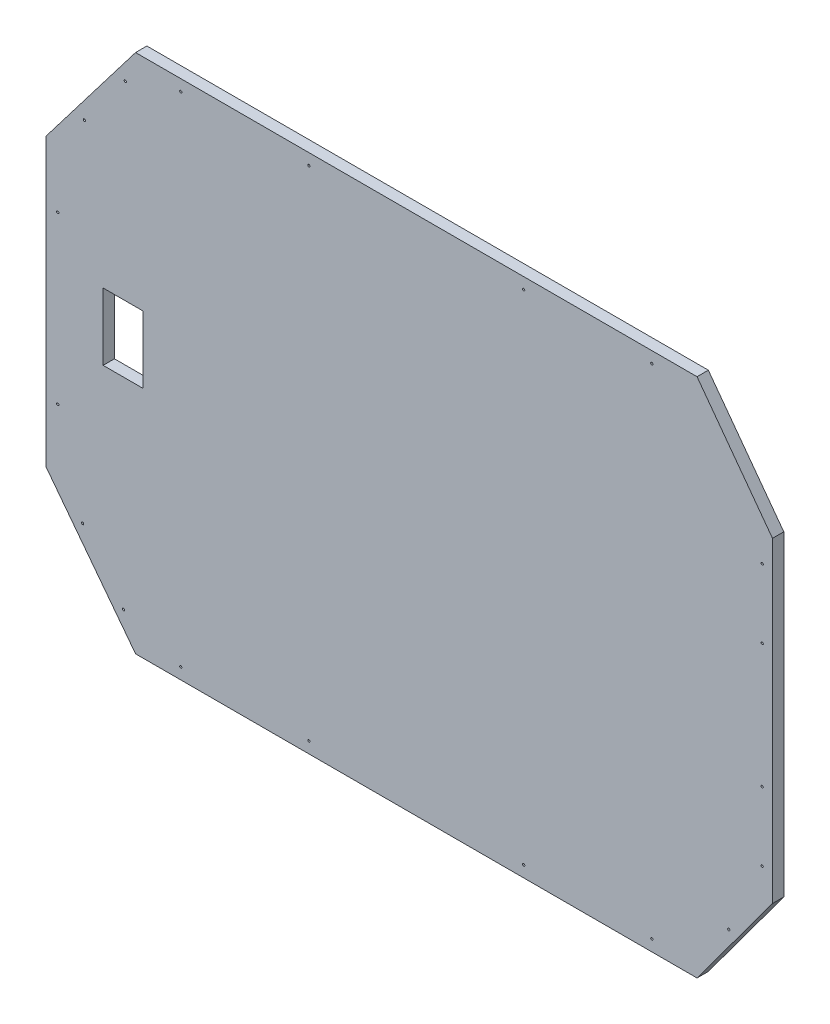
SolidWorks part; units mm, degrees
ref_plane "Front Plane" through (0, 0, 0) normal (0, 0, 1) x (1, 0, 0)
ref_plane "Top Plane" through (0, 0, 0) normal (0, 1, 0) x (1, 0, 0)
ref_plane "Right Plane" through (0, 0, 0) normal (1, 0, 0) x (0, 0, -1)
sketch "Sketch1" plane through (0, 0, 0) normal (0, 0, 1) x (1, 0, 0)
  line L0 (118.58, 345.4877) -> (863.58, 345.4877) construction
  line L1 (0, 500.6804) -> (118.58, 345.4877) construction
  line L2 (0, 881.2704) -> (0, 500.6804) construction
  line L3 (118.58, 1036.4632) -> (0, 881.2704) construction
  line L4 (863.58, 1036.4632) -> (118.58, 1036.4632) construction
  line L5 (963.71, 900.8043) -> (863.58, 1036.4632) construction
  line L6 (963.71, 481.1465) -> (963.71, 900.8043) construction
  line L7 (863.58, 345.4877) -> (963.71, 481.1465) construction
  line L8 (118.58, 345.4877) -> (863.58, 345.4877)
  line L9 (0, 500.6804) -> (118.58, 345.4877)
  line L10 (0, 881.2704) -> (0, 500.6804)
  line L11 (118.58, 1036.4632) -> (0, 881.2704)
  line L12 (863.58, 1036.4632) -> (118.58, 1036.4632)
  line L13 (963.71, 900.8043) -> (863.58, 1036.4632)
  line L14 (963.71, 481.1465) -> (963.71, 900.8043)
  line L15 (863.58, 345.4877) -> (963.71, 481.1465)
  line L60 (44.2234, 939.1483) -> (2.5279, 884.5789)
  line L62 (44.2234, 939.1483) -> (2.5279, 884.5789)
  line L64 (2.5279, 884.5789) -> (2.5279, 710.9754)
  line L66 (2.5279, 884.5789) -> (2.5279, 710.9754)
  line L68 (2.5279, 710.9754) -> (32.5279, 710.9754)
  line L70 (52.236, 458.7868) -> (91.9659, 489.1436)
  line L71 (91.9659, 489.1436) -> (128.8173, 440.9139)
  line L72 (128.8173, 440.9139) -> (81.1415, 404.4857)
  line L73 (2.5279, 710.9754) -> (32.5279, 710.9754)
  line L75 (247.5279, 355.4877) -> (247.5279, 421.1462)
  line L76 (247.5279, 421.1462) -> (301.5406, 421.1462)
  line L77 (301.5406, 421.1462) -> (301.5406, 355.4877)
  line L78 (32.5279, 710.9754) -> (32.5279, 680.9754)
  line L80 (32.5279, 710.9754) -> (32.5279, 680.9754)
  line L82 (32.5279, 680.9754) -> (2.5279, 680.9754)
  line L83 (501.5406, 355.4877) -> (501.5406, 421.1462)
  line L84 (501.5406, 421.1462) -> (555.5406, 421.1462)
  line L85 (555.5406, 421.1462) -> (555.5406, 355.4877)
  line L87 (32.5279, 680.9754) -> (2.5279, 680.9754)
  line L88 (894.7004, 404.4193) -> (852.6416, 435.4629)
  line L89 (852.6416, 435.4629) -> (885.5391, 480.0333)
  line L90 (885.5391, 480.0333) -> (927.5979, 448.9897)
  line L92 (2.5279, 680.9754) -> (2.5279, 507.372)
  line L94 (2.5279, 680.9754) -> (2.5279, 507.372)
  line L96 (2.5279, 507.372) -> (44.2234, 452.8026)
  line L98 (927.5979, 942.9612) -> (885.5391, 911.9176)
  line L99 (885.5391, 911.9176) -> (852.6416, 956.4879)
  line L100 (852.6416, 956.4879) -> (894.7004, 987.5316)
  line L101 (2.5279, 507.372) -> (44.2234, 452.8026)
  line L103 (555.5406, 1036.4632) -> (555.5406, 970.8046)
  line L104 (555.5406, 970.8046) -> (501.5406, 970.8046)
  line L105 (501.5406, 970.8046) -> (501.5406, 1036.4632)
  line L106 (44.2234, 452.8026) -> (52.1694, 458.874)
  line L108 (44.2234, 452.8026) -> (52.1694, 458.874)
  line L110 (52.1694, 458.874) -> (52.236, 458.7868)
  line L111 (301.5406, 1036.4632) -> (301.5406, 970.8046)
  line L112 (301.5406, 970.8046) -> (247.5279, 970.8046)
  line L113 (247.5279, 970.8046) -> (247.5279, 1036.4632)
  line L115 (52.1694, 458.874) -> (52.236, 458.7868)
  line L116 (81.1415, 987.4652) -> (128.8173, 951.0369)
  line L117 (128.8173, 951.0369) -> (91.9659, 902.8072)
  line L118 (91.9659, 902.8072) -> (52.236, 933.1641)
  line L130 (52.236, 458.7868) -> (91.9659, 489.1436)
  line L131 (91.9659, 489.1436) -> (128.8173, 440.9139)
  line L132 (128.8173, 440.9139) -> (81.1415, 404.4857)
  line L135 (247.5279, 355.4877) -> (247.5279, 421.1462)
  line L136 (247.5279, 421.1462) -> (301.5406, 421.1462)
  line L137 (301.5406, 421.1462) -> (301.5406, 355.4877)
  line L143 (501.5406, 355.4877) -> (501.5406, 421.1462)
  line L144 (501.5406, 421.1462) -> (555.5406, 421.1462)
  line L145 (555.5406, 421.1462) -> (555.5406, 355.4877)
  line L148 (894.7004, 404.4193) -> (852.6416, 435.4629)
  line L149 (852.6416, 435.4629) -> (885.5391, 480.0333)
  line L150 (885.5391, 480.0333) -> (927.5979, 448.9897)
  line L158 (927.5979, 942.9612) -> (885.5391, 911.9176)
  line L159 (885.5391, 911.9176) -> (852.6416, 956.4879)
  line L160 (852.6416, 956.4879) -> (894.7004, 987.5316)
  line L163 (555.5406, 1036.4632) -> (555.5406, 970.8046)
  line L164 (555.5406, 970.8046) -> (501.5406, 970.8046)
  line L165 (501.5406, 970.8046) -> (501.5406, 1036.4632)
  line L171 (301.5406, 1036.4632) -> (301.5406, 970.8046)
  line L172 (301.5406, 970.8046) -> (247.5279, 970.8046)
  line L173 (247.5279, 970.8046) -> (247.5279, 1036.4632)
  line L176 (81.1415, 987.4652) -> (128.8173, 951.0369)
  line L177 (128.8173, 951.0369) -> (91.9659, 902.8072)
  line L178 (91.9659, 902.8072) -> (52.236, 933.1641)
  line L344 (81.1415, 404.4857) -> (118.58, 355.4877)
  line L346 (81.1415, 404.4857) -> (118.58, 355.4877)
  line L420 (118.58, 355.4877) -> (247.5279, 355.4877)
  line L421 (118.58, 355.4877) -> (247.5279, 355.4877)
  line L422 (301.5406, 355.4877) -> (439.5279, 355.4877)
  line L423 (301.5406, 355.4877) -> (439.5279, 355.4877)
  line L424 (439.5279, 355.4877) -> (439.5279, 385.4877)
  line L425 (439.5279, 355.4877) -> (439.5279, 385.4877)
  line L426 (439.5279, 385.4877) -> (469.5279, 385.4877)
  line L427 (439.5279, 385.4877) -> (469.5279, 385.4877)
  line L428 (469.5279, 385.4877) -> (469.5279, 355.4877)
  line L429 (469.5279, 385.4877) -> (469.5279, 355.4877)
  line L430 (469.5279, 355.4877) -> (501.5406, 355.4877)
  line L431 (469.5279, 355.4877) -> (501.5406, 355.4877)
  line L432 (555.5406, 355.4877) -> (858.5839, 355.4877)
  line L433 (555.5406, 355.4877) -> (858.5839, 355.4877)
  line L434 (858.5839, 355.4877) -> (894.7004, 404.4193)
  line L435 (858.5839, 355.4877) -> (894.7004, 404.4193)
  line L436 (927.5979, 448.9897) -> (956.2379, 487.792)
  line L437 (927.5979, 448.9897) -> (956.2379, 487.792)
  line L438 (956.2379, 487.792) -> (956.2379, 680.9754)
  line L439 (956.2379, 487.792) -> (956.2379, 680.9754)
  line L440 (956.2379, 680.9754) -> (926.2379, 680.9754)
  line L441 (956.2379, 680.9754) -> (926.2379, 680.9754)
  line L442 (926.2379, 680.9754) -> (926.2379, 710.9754)
  line L443 (926.2379, 680.9754) -> (926.2379, 710.9754)
  line L444 (926.2379, 710.9754) -> (956.2379, 710.9754)
  line L445 (926.2379, 710.9754) -> (956.2379, 710.9754)
  line L446 (956.2379, 710.9754) -> (956.2379, 904.1589)
  line L447 (956.2379, 710.9754) -> (956.2379, 904.1589)
  line L448 (956.2379, 904.1589) -> (927.5979, 942.9612)
  line L449 (956.2379, 904.1589) -> (927.5979, 942.9612)
  line L450 (894.7004, 987.5316) -> (858.5839, 1036.4632)
  line L451 (894.7004, 987.5316) -> (858.5839, 1036.4632)
  line L452 (858.5839, 1036.4632) -> (555.5406, 1036.4632)
  line L453 (858.5839, 1036.4632) -> (555.5406, 1036.4632)
  line L454 (501.5406, 1036.4632) -> (469.5279, 1036.4632)
  line L455 (501.5406, 1036.4632) -> (469.5279, 1036.4632)
  line L456 (469.5279, 1036.4632) -> (469.5279, 1006.4632)
  line L457 (469.5279, 1036.4632) -> (469.5279, 1006.4632)
  line L458 (469.5279, 1006.4632) -> (439.5279, 1006.4632)
  line L459 (469.5279, 1006.4632) -> (439.5279, 1006.4632)
  line L460 (439.5279, 1006.4632) -> (439.5279, 1036.4632)
  line L461 (439.5279, 1006.4632) -> (439.5279, 1036.4632)
  line L462 (439.5279, 1036.4632) -> (301.5406, 1036.4632)
  line L463 (439.5279, 1036.4632) -> (301.5406, 1036.4632)
  line L464 (247.5279, 1036.4632) -> (118.58, 1036.4632)
  line L465 (247.5279, 1036.4632) -> (118.58, 1036.4632)
  line L466 (118.58, 1036.4632) -> (81.1415, 987.4652)
  line L467 (118.58, 1036.4632) -> (81.1415, 987.4652)
  line L530 (52.1694, 933.0769) -> (44.2234, 939.1483)
  line L531 (52.1694, 933.0769) -> (44.2234, 939.1483)
  line L532 (52.236, 933.1641) -> (52.1694, 933.0769)
  line L533 (52.236, 933.1641) -> (52.1694, 933.0769)
  circle A0 centre (633.58, 360.4877) radius 1.5 construction
  circle A1 centre (348.58, 360.4877) radius 1.5 construction
  circle A2 centre (178.58, 360.4877) radius 1.5 construction
  arc A3 (101.5789, 389.644) -> (103.3851, 387.2486) centre (102.482, 388.4463) ccw construction
  arc A4 (103.3851, 387.2486) -> (101.5789, 389.644) centre (102.482, 388.4463) ccw construction
  arc A5 (49.1995, 459.109) -> (47.3933, 461.5044) centre (48.2964, 460.3067) ccw construction
  arc A6 (47.3933, 461.5044) -> (49.1995, 459.109) centre (48.2964, 460.3067) ccw construction
  arc A7 (15.3287, 579.1804) -> (15.3287, 582.1804) centre (15.3287, 580.6804) ccw construction
  arc A8 (15.3287, 582.1804) -> (15.3287, 579.1804) centre (15.3287, 580.6804) ccw construction
  arc A9 (15.3287, 799.7704) -> (15.3287, 802.7704) centre (15.3287, 801.2704) ccw construction
  arc A10 (15.3287, 802.7704) -> (15.3287, 799.7704) centre (15.3287, 801.2704) ccw construction
  arc A11 (51.6031, 926.0294) -> (49.7969, 923.6341) centre (50.7, 924.8318) ccw construction
  arc A12 (49.7969, 923.6341) -> (51.6031, 926.0294) centre (50.7, 924.8318) ccw construction
  arc A13 (105.7887, 997.8898) -> (103.9825, 995.4945) centre (104.8856, 996.6922) ccw construction
  arc A14 (103.9825, 995.4945) -> (105.7887, 997.8898) centre (104.8856, 996.6922) ccw construction
  circle A15 centre (178.58, 1021.4632) radius 1.5 construction
  circle A16 centre (348.58, 1021.4632) radius 1.5 construction
  circle A17 centre (633.58, 1021.4632) radius 1.5 construction
  circle A18 centre (803.58, 1021.4632) radius 1.5 construction
  circle A19 centre (905.6543, 959.6921) radius 1.5 construction
  circle A20 centre (950.0195, 864.7409) radius 1.5 construction
  circle A21 centre (950.0195, 773.3269) radius 1.5 construction
  circle A22 centre (950.0195, 608.6349) radius 1.5 construction
  circle A23 centre (950.0195, 517.2209) radius 1.5 construction
  circle A24 centre (803.58, 360.4877) radius 1.5 construction
  circle A25 centre (905.6543, 422.2697) radius 1.5 construction
  circle A26 centre (633.58, 360.4877) radius 1.5
  circle A27 centre (348.58, 360.4877) radius 1.5
  circle A28 centre (178.58, 360.4877) radius 1.5
  arc A29 (101.5789, 389.644) -> (103.3851, 387.2486) centre (102.482, 388.4463) ccw
  arc A30 (103.3851, 387.2486) -> (101.5789, 389.644) centre (102.482, 388.4463) ccw
  arc A31 (49.1995, 459.109) -> (47.3933, 461.5044) centre (48.2964, 460.3067) ccw
  arc A32 (47.3933, 461.5044) -> (49.1995, 459.109) centre (48.2964, 460.3067) ccw
  arc A33 (15.3287, 579.1804) -> (15.3287, 582.1804) centre (15.3287, 580.6804) ccw
  arc A34 (15.3287, 582.1804) -> (15.3287, 579.1804) centre (15.3287, 580.6804) ccw
  arc A35 (15.3287, 799.7704) -> (15.3287, 802.7704) centre (15.3287, 801.2704) ccw
  arc A36 (15.3287, 802.7704) -> (15.3287, 799.7704) centre (15.3287, 801.2704) ccw
  arc A37 (51.6031, 926.0294) -> (49.7969, 923.6341) centre (50.7, 924.8318) ccw
  arc A38 (49.7969, 923.6341) -> (51.6031, 926.0294) centre (50.7, 924.8318) ccw
  arc A39 (105.7887, 997.8898) -> (103.9825, 995.4945) centre (104.8856, 996.6922) ccw
  arc A40 (103.9825, 995.4945) -> (105.7887, 997.8898) centre (104.8856, 996.6922) ccw
  circle A41 centre (178.58, 1021.4632) radius 1.5
  circle A42 centre (348.58, 1021.4632) radius 1.5
  circle A43 centre (633.58, 1021.4632) radius 1.5
  circle A44 centre (803.58, 1021.4632) radius 1.5
  circle A45 centre (905.6543, 959.6921) radius 1.5
  circle A46 centre (950.0195, 864.7409) radius 1.5
  circle A47 centre (950.0195, 773.3269) radius 1.5
  circle A48 centre (950.0195, 608.6349) radius 1.5
  circle A49 centre (950.0195, 517.2209) radius 1.5
  circle A50 centre (803.58, 360.4877) radius 1.5
  circle A51 centre (905.6543, 422.2697) radius 1.5
  dimension "D1" = 0
sketch "Sketch2" plane through (0, 0, 0) normal (0, 0, 1) x (1, 0, 0)
  line L0 (0, 500.6804) -> (118.58, 345.4877) construction
  line L1 (118.58, 345.4877) -> (863.58, 345.4877) construction
  line L2 (863.58, 345.4877) -> (963.71, 481.1465) construction
  line L3 (963.71, 481.1465) -> (963.71, 900.8043) construction
  line L4 (963.71, 900.8043) -> (863.58, 1036.4632) construction
  line L5 (863.58, 1036.4632) -> (118.58, 1036.4632) construction
  line L6 (118.58, 1036.4632) -> (0, 881.2704) construction
  line L7 (0, 881.2704) -> (0, 500.6804) construction
  line L8 (0, 500.6804) -> (118.58, 345.4877)
  line L9 (118.58, 345.4877) -> (863.58, 345.4877)
  line L10 (863.58, 345.4877) -> (963.71, 481.1465)
  line L11 (963.71, 481.1465) -> (963.71, 900.8043)
  line L12 (963.71, 900.8043) -> (863.58, 1036.4632)
  line L13 (863.58, 1036.4632) -> (118.58, 1036.4632)
  line L14 (118.58, 1036.4632) -> (0, 881.2704)
  line L15 (0, 881.2704) -> (0, 500.6804)
extrude "Boss-Extrude1" add sketch "Sketch2" along normal blind 15
sketch "Sketch7" plane through (0, 0, 0) normal (0, 0, -1) x (-1, 0, 0)
  line L8 (0, 500.6804) -> (0, 881.2704)
  line L9 (0, 881.2704) -> (-118.58, 1036.4632)
  line L10 (-118.58, 1036.4632) -> (-863.58, 1036.4632)
  line L11 (-863.58, 1036.4632) -> (-963.71, 900.8043)
  line L12 (-963.71, 900.8043) -> (-963.71, 481.1465)
  line L13 (-963.71, 481.1465) -> (-863.58, 345.4877)
  line L14 (-863.58, 345.4877) -> (-118.58, 345.4877)
  line L15 (-118.58, 345.4877) -> (0, 500.6804)
  line L16 (0, 500.6804) -> (0, 881.2704)
  line L17 (0, 881.2704) -> (-118.58, 1036.4632)
  line L18 (-118.58, 1036.4632) -> (-863.58, 1036.4632)
  line L19 (-863.58, 1036.4632) -> (-963.71, 900.8043)
  line L20 (-963.71, 900.8043) -> (-963.71, 481.1465)
  line L21 (-963.71, 481.1465) -> (-863.58, 345.4877)
  line L22 (-863.58, 345.4877) -> (-118.58, 345.4877)
  line L23 (-118.58, 345.4877) -> (0, 500.6804)
  circle A0 centre (-950.0195, 773.3269) radius 1.5 construction
  circle A1 centre (-950.0195, 773.3269) radius 1.5
  arc A2 (-15.3287, 579.1804) -> (-15.3287, 582.1804) centre (-15.3287, 580.6804) ccw construction
  arc A3 (-15.3287, 582.1804) -> (-15.3287, 579.1804) centre (-15.3287, 580.6804) ccw construction
  arc A4 (-47.3933, 461.5044) -> (-49.1995, 459.109) centre (-48.2964, 460.3067) ccw construction
  arc A5 (-101.5789, 389.644) -> (-103.3851, 387.2486) centre (-102.482, 388.4463) ccw construction
  arc A6 (-103.3851, 387.2486) -> (-101.5789, 389.644) centre (-102.482, 388.4463) ccw construction
  circle A7 centre (-178.58, 360.4877) radius 1.5 construction
  circle A8 centre (-348.58, 360.4877) radius 1.5 construction
  circle A9 centre (-633.58, 360.4877) radius 1.5 construction
  circle A10 centre (-803.58, 360.4877) radius 1.5 construction
  circle A11 centre (-905.6543, 422.2697) radius 1.5 construction
  circle A12 centre (-950.0195, 517.2209) radius 1.5 construction
  circle A13 centre (-950.0195, 608.6349) radius 1.5 construction
  circle A14 centre (-950.0195, 864.7409) radius 1.5 construction
  arc A15 (-15.3287, 579.1804) -> (-15.3287, 582.1804) centre (-15.3287, 580.6804) ccw
  arc A16 (-15.3287, 582.1804) -> (-15.3287, 579.1804) centre (-15.3287, 580.6804) ccw
  arc A17 (-47.3933, 461.5044) -> (-49.1995, 459.109) centre (-48.2964, 460.3067) ccw
  arc A18 (-101.5789, 389.644) -> (-103.3851, 387.2486) centre (-102.482, 388.4463) ccw
  arc A19 (-103.3851, 387.2486) -> (-101.5789, 389.644) centre (-102.482, 388.4463) ccw
  circle A20 centre (-178.58, 360.4877) radius 1.5
  circle A21 centre (-348.58, 360.4877) radius 1.5
  circle A22 centre (-633.58, 360.4877) radius 1.5
  circle A23 centre (-803.58, 360.4877) radius 1.5
  circle A24 centre (-905.6543, 422.2697) radius 1.5
  circle A25 centre (-950.0195, 517.2209) radius 1.5
  circle A26 centre (-950.0195, 608.6349) radius 1.5
  circle A27 centre (-950.0195, 864.7409) radius 1.5
  point P8 (-47.3933, 461.5044)
  point P10 (-48.2964, 460.3067)
  point P12 (-102.482, 388.4463)
  point P14 (-103.3851, 387.2486)
  point P15 (-950.0195, 864.7409)
  dimension "D1" = 0
sketch "Sketch9" plane through (0, 0, 0) normal (0, 0, -1) x (-1, 0, 0)
  circle A0 centre (-803.58, 1021.4632) radius 1.5 construction
  circle A1 centre (-633.58, 1021.4632) radius 1.5 construction
  circle A2 centre (-348.58, 1021.4632) radius 1.5 construction
  circle A3 centre (-178.58, 1021.4632) radius 1.5 construction
  arc A4 (-49.7969, 923.6341) -> (-51.6031, 926.0294) centre (-50.7, 924.8318) ccw construction
  arc A5 (-51.6031, 926.0294) -> (-49.7969, 923.6341) centre (-50.7, 924.8318) ccw construction
  arc A6 (-103.9825, 995.4945) -> (-105.7887, 997.8898) centre (-104.8856, 996.6922) ccw construction
  arc A7 (-105.7887, 997.8898) -> (-103.9825, 995.4945) centre (-104.8856, 996.6922) ccw construction
  arc A8 (-15.3287, 802.7704) -> (-15.3287, 799.7704) centre (-15.3287, 801.2704) ccw construction
  arc A9 (-15.3287, 799.7704) -> (-15.3287, 802.7704) centre (-15.3287, 801.2704) ccw construction
  arc A10 (-15.3287, 582.1804) -> (-15.3287, 579.1804) centre (-15.3287, 580.6804) ccw construction
  arc A11 (-15.3287, 579.1804) -> (-15.3287, 582.1804) centre (-15.3287, 580.6804) ccw construction
  arc A12 (-49.1995, 459.109) -> (-47.3933, 461.5044) centre (-48.2964, 460.3067) ccw construction
  arc A13 (-47.3933, 461.5044) -> (-49.1995, 459.109) centre (-48.2964, 460.3067) ccw construction
  arc A14 (-103.3851, 387.2486) -> (-101.5789, 389.644) centre (-102.482, 388.4463) ccw construction
  arc A15 (-101.5789, 389.644) -> (-103.3851, 387.2486) centre (-102.482, 388.4463) ccw construction
  circle A16 centre (-178.58, 360.4877) radius 1.5 construction
  circle A17 centre (-348.58, 360.4877) radius 1.5 construction
  circle A18 centre (-633.58, 360.4877) radius 1.5 construction
  circle A19 centre (-803.58, 360.4877) radius 1.5 construction
  circle A20 centre (-905.6543, 422.2697) radius 1.5 construction
  circle A21 centre (-950.0195, 517.2209) radius 1.5 construction
  circle A22 centre (-950.0195, 864.7409) radius 1.5 construction
  circle A23 centre (-950.0195, 773.3269) radius 1.5 construction
  circle A24 centre (-950.0195, 608.6349) radius 1.5 construction
  circle A25 centre (-803.58, 1021.4632) radius 1.5
  circle A26 centre (-633.58, 1021.4632) radius 1.5
  circle A27 centre (-348.58, 1021.4632) radius 1.5
  circle A28 centre (-178.58, 1021.4632) radius 1.5
  arc A29 (-49.7969, 923.6341) -> (-51.6031, 926.0294) centre (-50.7, 924.8318) ccw
  arc A30 (-51.6031, 926.0294) -> (-49.7969, 923.6341) centre (-50.7, 924.8318) ccw
  arc A31 (-103.9825, 995.4945) -> (-105.7887, 997.8898) centre (-104.8856, 996.6922) ccw
  arc A32 (-105.7887, 997.8898) -> (-103.9825, 995.4945) centre (-104.8856, 996.6922) ccw
  arc A33 (-15.3287, 802.7704) -> (-15.3287, 799.7704) centre (-15.3287, 801.2704) ccw
  arc A34 (-15.3287, 799.7704) -> (-15.3287, 802.7704) centre (-15.3287, 801.2704) ccw
  arc A35 (-15.3287, 582.1804) -> (-15.3287, 579.1804) centre (-15.3287, 580.6804) ccw
  arc A36 (-15.3287, 579.1804) -> (-15.3287, 582.1804) centre (-15.3287, 580.6804) ccw
  arc A37 (-49.1995, 459.109) -> (-47.3933, 461.5044) centre (-48.2964, 460.3067) ccw
  arc A38 (-47.3933, 461.5044) -> (-49.1995, 459.109) centre (-48.2964, 460.3067) ccw
  arc A39 (-103.3851, 387.2486) -> (-101.5789, 389.644) centre (-102.482, 388.4463) ccw
  arc A40 (-101.5789, 389.644) -> (-103.3851, 387.2486) centre (-102.482, 388.4463) ccw
  circle A41 centre (-178.58, 360.4877) radius 1.5
  circle A42 centre (-348.58, 360.4877) radius 1.5
  circle A43 centre (-633.58, 360.4877) radius 1.5
  circle A44 centre (-803.58, 360.4877) radius 1.5
  circle A45 centre (-905.6543, 422.2697) radius 1.5
  circle A46 centre (-950.0195, 517.2209) radius 1.5
  circle A47 centre (-950.0195, 864.7409) radius 1.5
  circle A48 centre (-950.0195, 773.3269) radius 1.5
  circle A49 centre (-950.0195, 608.6349) radius 1.5
  point P2 (-950.0195, 517.2209)
extrude "Cut-Extrude1" cut sketch "Sketch9" against normal through all and the other way through all
sketch "Sketch10" plane through (0, 0, 0) normal (0, 0, -1) x (-1, 0, 0)
  line L0 (0, 881.2704) -> (0, 500.6804) construction
  line L1 (-128.15, 744.3942) -> (-75.55, 744.3942)
  line L2 (-128.15, 744.3942) -> (-128.15, 655.4942)
  line L3 (-128.15, 655.4942) -> (-75.55, 655.4942)
  line L4 (-75.55, 744.3942) -> (-75.55, 655.4942)
  line L5 (-118.58, 345.4877) -> (-863.58, 345.4877) construction
  dimension "D1" = 52.6
  dimension "D2" = 88.9
  dimension "D3" = 75.55
  dimension "D4" = 310.0065
extrude "Cut-Extrude2" cut sketch "Sketch10" against normal through all
